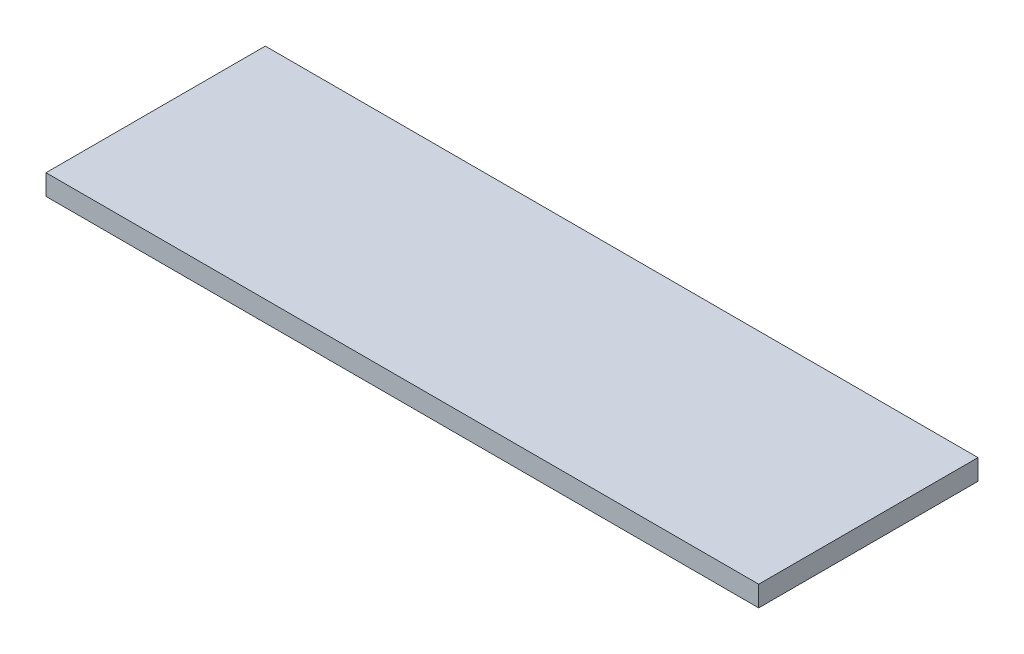
SolidWorks part; units mm, degrees
ref_plane "Front Plane" through (0, 0, 0) normal (0, 0, 1) x (1, 0, 0)
ref_plane "Top Plane" through (0, 0, 0) normal (0, 1, 0) x (1, 0, 0)
ref_plane "Right Plane" through (0, 0, 0) normal (1, 0, 0) x (0, 0, -1)
sketch "Sketch1" plane through (0, 0, 0) normal (0, 1, 0) x (1, 0, 0)
  line L1 (0, 0) -> (165.1, 0)
  line L2 (0, 0) -> (0, -50.8)
  line L3 (0, -50.8) -> (165.1, -50.8)
  line L4 (165.1, 0) -> (165.1, -50.8)
  dimension "D1" = 50.8
  dimension "D2" = 165.1
extrude "Boss-Extrude1" add sketch "Sketch1" along normal blind 4.7625 contours L1 L4 L3 L2
